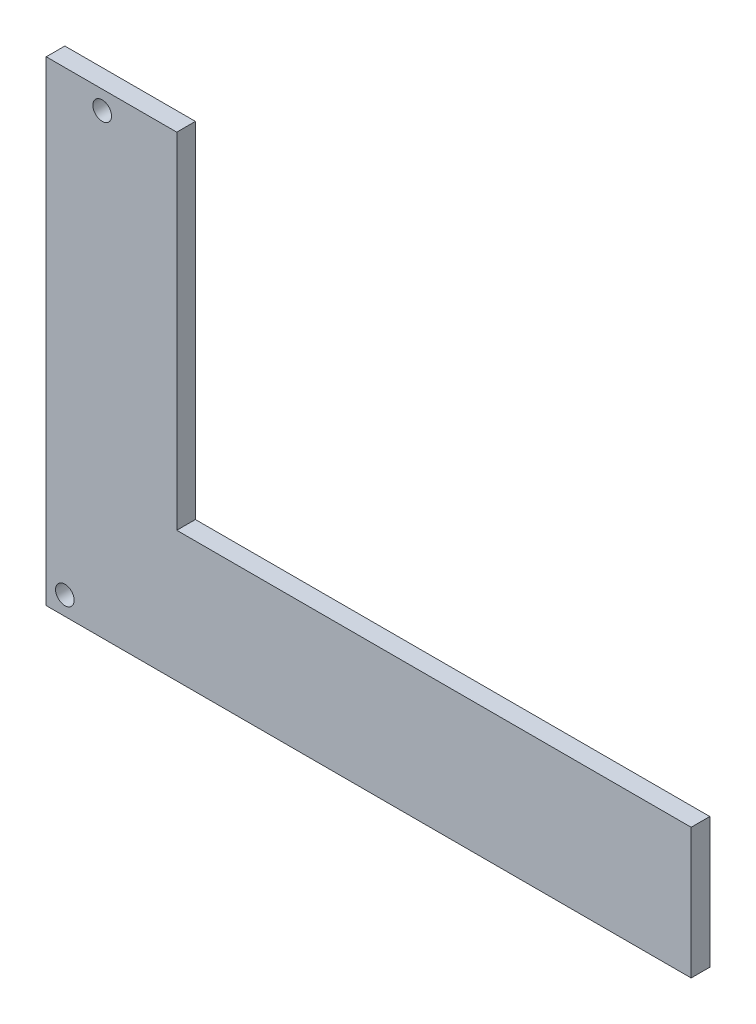
SolidWorks part; units mm, degrees
ref_plane "Front Plane" through (0, 0, 0) normal (0, 0, 1) x (1, 0, 0)
ref_plane "Top Plane" through (0, 0, 0) normal (0, 1, 0) x (1, 0, 0)
ref_plane "Right Plane" through (0, 0, 0) normal (1, 0, 0) x (0, 0, -1)
sketch "Sketch2" plane through (0, 0, 0) normal (0, 0, 1) x (1, 0, 0)
  line L14 (-18, 109.5077) -> (17.0187, 109.5077)
  line L15 (-18, 109.5077) -> (-18, -18)
  line L16 (-18, -18) -> (155, -18)
  line L17 (155, -18) -> (155, 17.0179)
  line L19 (17.0187, 17.0179) -> (17.0187, 109.5077)
  line L20 (17.0187, 17.0179) -> (155, 17.0179)
  point P30 (13.4831, 13.4825)
  dimension "D6" = 5
extrude "Boss-Extrude1" add sketch "Sketch2" along normal blind 5
sketch "Sketch3" plane through (0, 0, 5) normal (0, 0, 1) x (1, 0, 0)
  line L0 (-18, -18) -> (155, -18) construction
  line L1 (-18, 109.5077) -> (-18, -18) construction
  line L2 (17.0187, 109.5077) -> (-18, 109.5077) construction
  line L3 (17.0187, 17.0179) -> (17.0187, 109.5077) construction
  circle A0 centre (-13, -13) radius 2.5
  circle A1 centre (-2.9813, 104.5077) radius 2.5
  dimension "D1" = 5
  dimension "D2" = 5
  dimension "D3" = 5
  dimension "D4" = 5
  dimension "D5" = 5
  dimension "D6" = 20
extrude "Cut-Extrude1" cut sketch "Sketch3" against normal through all
